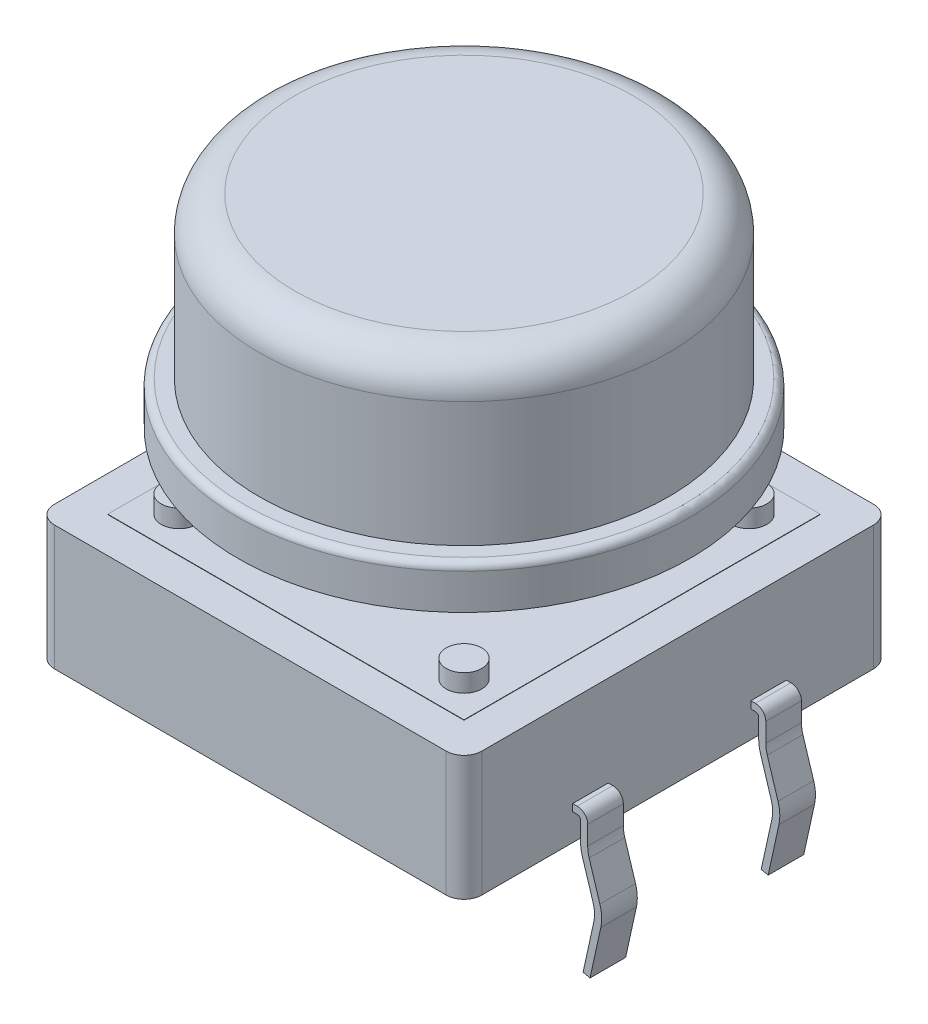
SolidWorks part; units mm, degrees
ref_plane "Plan de face" through (0, 0, 0) normal (0, 0, 1) x (1, 0, 0)
ref_plane "Plan de dessus" through (0, 0, 0) normal (0, 1, 0) x (1, 0, 0)
ref_plane "Plan de droite" through (0, 0, 0) normal (1, 0, 0) x (0, 0, -1)
sketch "Esquisse1" plane through (0, 0, 0) normal (0, 1, 0) x (1, 0, 0)
  line L0 (0, 75.956) -> (0, -64.1064) construction
  line L1 (-70.8607, 0) -> (78.6814, 0) construction
  line L2 (-6, 43.4881) -> (-6, -24.2917) construction
  line L3 (-33.1789, -6) -> (40.2887, -6) construction
  line L5 (-5.5, -6) -> (5.5, -6)
  line L6 (-6, -5.5) -> (-6, 5.5)
  line L7 (-5.5, 6) -> (5.5, 6)
  line L8 (6, -5.5) -> (6, 5.5)
  arc A0 (5.5, 6) -> (6, 5.5) centre (5.5, 5.5) cw
  arc A1 (-6, 5.5) -> (-5.5, 6) centre (-5.5, 5.5) cw
  arc A2 (-5.5, -6) -> (-6, -5.5) centre (-5.5, -5.5) cw
  arc A3 (5.5, -6) -> (6, -5.5) centre (5.5, -5.5) ccw
  dimension "D1" = 0.5
extrude "Extrusion2" add sketch "Esquisse1" along normal blind 3.5
sketch "Esquisse2" plane through (0, 3.5, 0) normal (0, 1, 0) x (-1, 0, 0)
  line L0 (6.7911, 0) -> (-7.1423, 0) construction
  line L1 (0, -6.3886) -> (0, 6.3593) construction
  line L2 (5, -6.3886) -> (5, 6.4471) construction
  line L3 (6.7911, 5) -> (-6.9374, 5) construction
  line L7 (5, 5) -> (-5, 5)
  line L8 (5, 5) -> (5, -5)
  line L9 (5, -5) -> (-5, -5)
  line L10 (-5, 5) -> (-5, -5)
extrude "Extrusion5" add sketch "Esquisse2" along normal blind 0.01
sketch "Esquisse6" plane through (0, 3.51, 0) normal (0, 1, 0) x (-1, 0, 0)
  line L0 (2.1661, 0) -> (-3.1321, 0) construction
  line L1 (0, 2.2613) -> (0, -2.1149) construction
  circle A0 centre (4, 4) radius 0.5
  circle A1 centre (-4, 4) radius 0.5
  circle A2 centre (-4, -4) radius 0.5
  circle A3 centre (4, -4) radius 0.5
extrude "Extrusion6" add sketch "Esquisse6" along normal blind 0.5
sketch "Esquisse7" plane through (0, 3.51, 0) normal (0, 1, 0) x (-1, 0, 0)
  circle A0 centre (0, 0) radius 3.05
extrude "Extrusion7" add sketch "Esquisse7" along normal blind 0.8
ref_plane "Plan2" through (-6.05, 0, 0) normal (-1, 0, 0) x (0, 0, 1)
sketch "Esquisse10" plane through (-6.05, 0, 0) normal (-1, 0, 0) x (0, 0, 1)
  line L0 (0, 5.3305) -> (0, -1.7343) construction
  line L1 (2.5, -2.0246) -> (2.5, 2.524) construction
  line L3 (1.9043, 0.8) -> (3.3197, 0.8) construction
  line L4 (1.9043, 1) -> (3.3197, 1) construction
  line L5 (3, 0.2739) -> (3, 1.411) construction
  line L6 (2, 0.2739) -> (2, 1.29) construction
  line L7 (-5.5, 0) -> (5.5, 0) construction
  line L8 (2.2786, 0.9) -> (2.8752, 0.9) construction
  line L10 (2, 1) -> (3, 1)
  line L11 (2, 1) -> (2, 0.8)
  line L12 (2, 0.8) -> (3, 0.8)
  line L13 (3, 1) -> (3, 0.8)
  dimension "D1" = 2.5
  dimension "D2" = 1
  dimension "D3" = 0.2
  dimension "D4" = 0.5
  dimension "D5" = 1
  dimension "D6" = 0.1
sketch3d "Esquisse3D4"
  line L0 (-6.0509, 0.9062, 2.5052) -> (-6.1782, 0.9062, 2.5052)
  line L1 (-6.3782, 0.7063, 2.5052) -> (-6.3784, 0.1762, 2.5052)
  line L2 (-6.4237, -0.1208, 2.5052) -> (-6.7258, -1.09, 2.5052)
  line L3 (-6.7478, -1.6019, 2.5052) -> (-6.4458, -2.9776, 2.5052)
  arc A0 (-6.7258, -1.09, 2.5052) -> (-6.7478, -1.6019, 2.5052) centre (-5.771, -1.3875, 2.5052) ccw
  arc A1 (-6.3784, 0.1762, 2.5052) -> (-6.4237, -0.1208, 2.5052) centre (-7.3784, 0.1767, 2.5052) ccw
  arc A2 (-6.1782, 0.9062, 2.5052) -> (-6.3782, 0.7063, 2.5052) centre (-6.1782, 0.7062, 2.5052) ccw
  point P6 (-6.8046, -1.343, 2.5052)
  point P7 (-5.771, -1.3875, 3.5052)
  point P10 (-6.3785, 0.0242, 2.5052)
  point P12 (-7.3784, 0.1767, 1.5052)
  point P18 (-6.3781, 0.9062, 2.5052)
  point P19 (-6.1782, 0.7062, 2.7052)
  dimension "D1" = 1
  dimension "D2" = 1
  dimension "D3" = 0.2
sweep "Balayage2" add profiles "Esquisse10" path "Esquisse3D4"
sketch "Esquisse11" plane through (0, 0, 0) normal (1, 0, 0) x (0, 0, -1)
  line L0 (-8.076, 4.31) -> (10.4231, 4.31) construction
  line L1 (0, -2.8388) -> (0, 12.0865) construction
  line L2 (-2.7, 7.8937) -> (-2.7, 2.0278) construction
  line L3 (-5.75, 12.0865) -> (-5.75, 4.9608) construction
  line L4 (-6.35, 8.0147) -> (-6.35, 4.9608) construction
  line L5 (5.9981, 11.31) -> (-8.2535, 11.31) construction
  line L6 (-9.2614, 5.61) -> (-1.1277, 5.61) construction
  line L7 (-7.0037, 6.81) -> (-4.484, 6.81) construction
  line L8 (0, 11.31) -> (-4.75, 11.31)
  line L9 (-5.75, 10.31) -> (-5.75, 6.81)
  line L10 (-5.75, 6.81) -> (-6.15, 6.81)
  line L11 (-6.35, 6.61) -> (-6.35, 5.61)
  line L12 (-6.35, 5.61) -> (-2.7, 5.61)
  line L13 (-2.7, 5.61) -> (-2.7, 4.31)
  line L14 (-2.7, 4.31) -> (0, 4.31)
  line L15 (0, 4.31) -> (0, 11.31)
  arc A0 (-4.75, 11.31) -> (-5.75, 10.31) centre (-4.75, 10.31) ccw
  arc A1 (-6.15, 6.81) -> (-6.35, 6.61) centre (-6.15, 6.61) ccw
  dimension "D7" = 1
  dimension "D8" = 0.2
  dimension "D1" = 1.3
  dimension "D2" = 5.75
  dimension "D3" = 5.7
  dimension "D4" = 1.2
  dimension "D5" = 0.6
  dimension "D6" = 2.7
revolve "Révolution2" add sketch "Esquisse11" angle 360 about L15
ref_plane "Plan3" through (0, 0, 0) normal (-1, 0, 0) x (0, 0, 1)
ref_plane "Plan4" through (0, 0, 0) normal (0, 0, -1) x (-1, 0, 0)
mirror "Symétrie2" about plane through (0, 0, 0) normal (0, 0, -1) of bodies 111 115
mirror "Symétrie3" about plane through (0, 0, 0) normal (-1, 0, 0) of bodies 116 111 114
